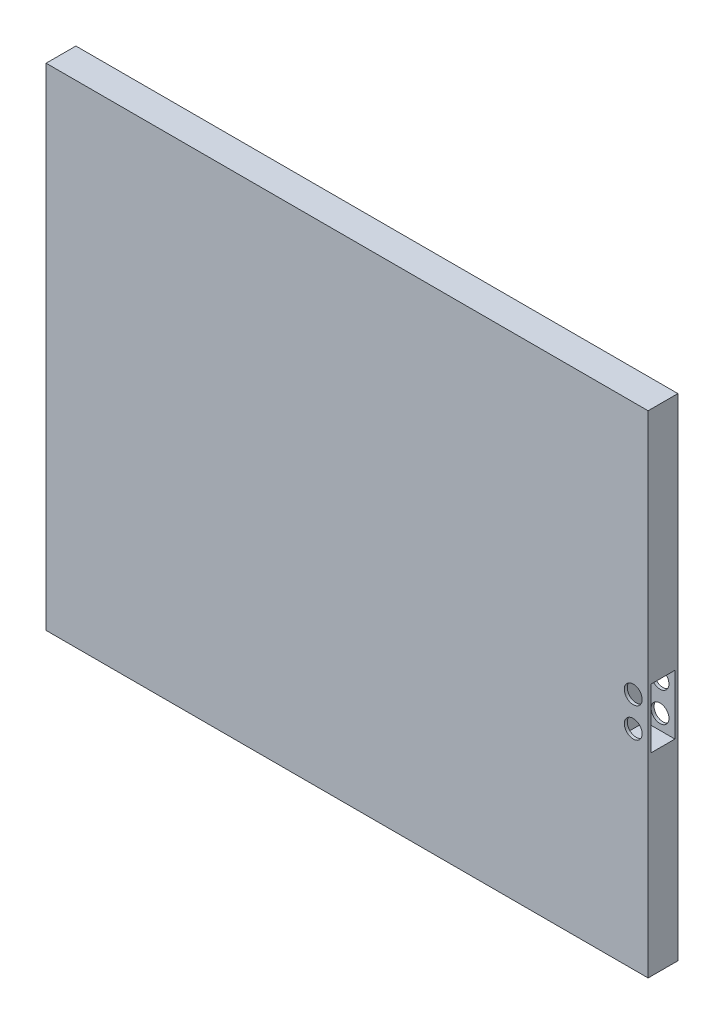
SolidWorks part; units mm, degrees
material "Polyurethane Foam Flexible"
ref_plane "Front Plane" through (0, 0, 0) normal (0, 0, 1) x (1, 0, 0)
ref_plane "Top Plane" through (0, 0, 0) normal (0, 1, 0) x (1, 0, 0)
ref_plane "Right Plane" through (0, 0, 0) normal (1, 0, 0) x (0, 0, -1)
sketch "Sketch1" plane through (0, 0, 0) normal (0, 0, 1) x (1, 0, 0)
  line L1 (-78.2272, 89.1981) -> (178.5668, 89.1981)
  line L2 (-78.2272, 89.1981) -> (-78.2272, -107.6519)
  line L3 (-78.2272, -107.6519) -> (178.5668, -107.6519)
  line L4 (178.5668, 89.1981) -> (178.5668, -107.6519)
  dimension "D1" = 196.85
  dimension "D2" = 256.794
extrude "Boss-Extrude1" add sketch "Sketch1" along normal blind 12.7
sketch "Sketch2" plane through (178.5668, 0, 0) normal (1, 0, 0) x (0, 0, -1)
  line L1 (-11.43, 0.3061) -> (-1.27, 0.3061)
  line L2 (-11.43, 0.3061) -> (-11.43, -25.0939)
  line L3 (-11.43, -25.0939) -> (-1.27, -25.0939)
  line L4 (-1.27, 0.3061) -> (-1.27, -25.0939)
  line L6 (-12.7, -107.6519) -> (-12.7, 89.1981) construction
  point P6 (-6.35, 0.3061)
  point P8 (-1.27, -12.3939)
  dimension "D1" = 25.4
  dimension "D2" = 101.6
  dimension "D3" = 10.16
  dimension "D4" = 6.35
extrude "Cut-Extrude1" cut sketch "Sketch2" against normal blind 12.7
sketch "Sketch3" plane through (0, 0, 12.7) normal (0, 0, 1) x (1, 0, 0)
  line L2 (178.5668, -107.6519) -> (178.5668, 89.1981) construction
  line L4 (165.8668, 0.3061) -> (178.5668, 0.3061) construction
  circle A1 centre (172.2168, -6.0439) radius 3.81
  circle A2 centre (172.2168, -18.7439) radius 3.81
  dimension "D3" = 6.35
  dimension "D5" = 7.62
  dimension "D4" = 6.35
  dimension "D6" = 2
extrude "Cut-Extrude2" cut sketch "Sketch3" against normal blind 12.7
sketch "Sketch4" plane through (0, 89.1981, 0) normal (0, 1, 0) x (1, 0, 0)
  line L1 (-78.2272, 0) -> (178.5668, 0)
  line L2 (-78.2272, 0) -> (-78.2272, -12.7)
  line L3 (-78.2272, -12.7) -> (178.5668, -12.7)
  line L4 (178.5668, 0) -> (178.5668, -12.7)
extrude "Boss-Extrude2" add sketch "Sketch4" along normal blind 12.7
